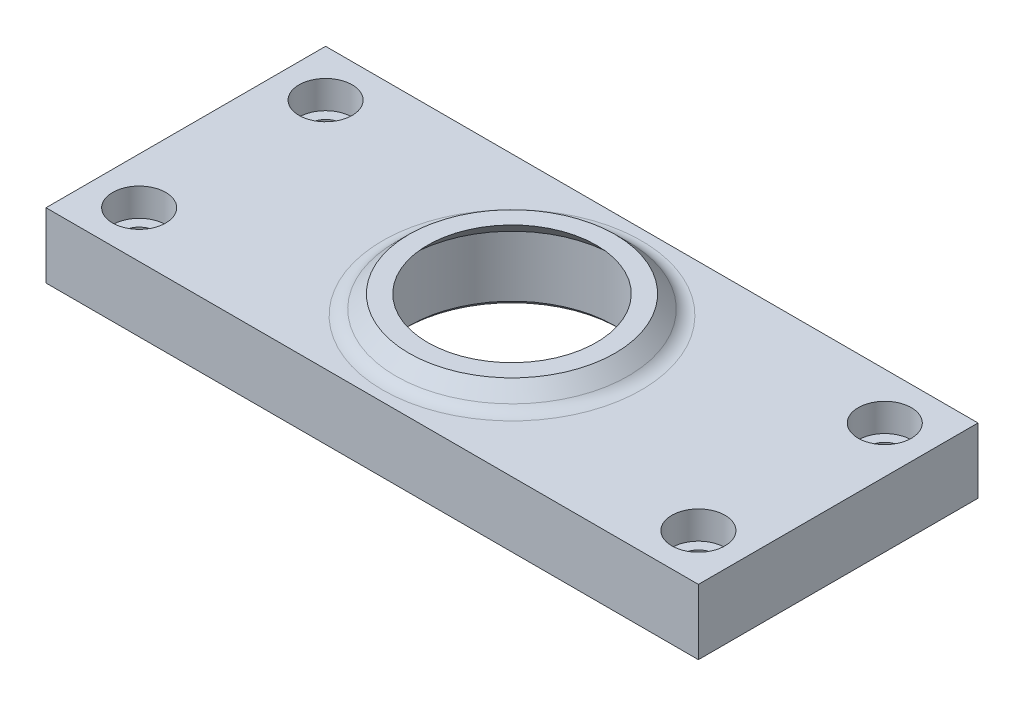
SolidWorks part; units mm, degrees
ref_plane "Front Plane" through (0, 0, 0) normal (0, 0, 1) x (1, 0, 0)
ref_plane "Top Plane" through (0, 0, 0) normal (0, 1, 0) x (1, 0, 0)
ref_plane "Right Plane" through (0, 0, 0) normal (1, 0, 0) x (0, 0, -1)
sketch "Sketch1" plane through (0, 0, 0) normal (0, 1, 0) x (1, 0, 0)
  circle A0 centre (0, 0) radius 11.05
  circle A1 centre (0, 0) radius 15
  dimension "D1" = 22.1
  dimension "D2" = 30
extrude "Boss-Extrude1" add sketch "Sketch1" along normal blind 7
sketch "Sketch2" plane through (0, 7, 0) normal (0, 1, 0) x (1, 0, 0)
  line L0 (0, -15) -> (-35, -15)
  line L1 (-35, -15) -> (-35, 15)
  line L2 (-35, 15) -> (0, 15)
  circle A0 centre (0, 0) radius 15 construction
  circle A2 centre (0, 0) radius 15
  arc A3 (0, 15) -> (0, -15) centre (0, 0) ccw
  dimension "D1" = 35
  dimension "D2" = 0
extrude "Boss-Extrude2" add sketch "Sketch2" against normal up to surface (7 mm away) up to face at (0, 0, 15)
sketch "Sketch3" plane through (0, 7, 0) normal (0, 1, 0) x (1, 0, 0)
  line L0 (-30, -15) -> (-30, 15) construction
  line L1 (-35, -15) -> (0, -15) construction
  line L2 (0, 15) -> (-35, 15) construction
  line L3 (-35, 15) -> (-35, -15) construction
  circle A0 centre (-30, 10) radius 1.7
  circle A1 centre (-30, -10) radius 1.7
  dimension "D1" = 3.4
  dimension "D2" = 5
  dimension "D3" = 5
  dimension "D4" = 5
extrude "Cut-Extrude1" cut sketch "Sketch3" against normal through all
sketch "Sketch4" plane through (0, 7, 0) normal (0, 1, 0) x (1, 0, 0)
  circle A0 centre (-30, 10) radius 2.85
  circle A1 centre (-30, -10) radius 2.85
  dimension "D1" = 5.7
extrude "Cut-Extrude2" cut sketch "Sketch4" against normal blind 3
fillet "Fillet1" [suppressed] radius 5
mirror "Mirror1" about plane through (0, 0, 0) normal (1, 0, 0) of "Boss-Extrude2", "Cut-Extrude1", "Cut-Extrude2"
sketch "Sketch6" plane through (0, 0, 0) normal (0, 0, 1) x (1, 0, 0)
  line L0 (11.05, 7) -> (9.05, 9)
  line L1 (9.05, 9) -> (11.05, 9)
  line L3 (11.05, 9) -> (13.05, 7)
  line L4 (13.05, 7) -> (11.05, 7)
  dimension "D1" = 2
  dimension "D2" = 2
  dimension "D3" = 135
revolve "Revolve1" add sketch "Sketch6" angle 360 about axis through (0, 7, 0) along (0, -1, 0)
fillet "Fillet2" radius 2 1 edges at (0, 7, 13.05)
chamfer "Chamfer1" distance 0.5 angle 45 1 edges at (0, 0, 11.05)
